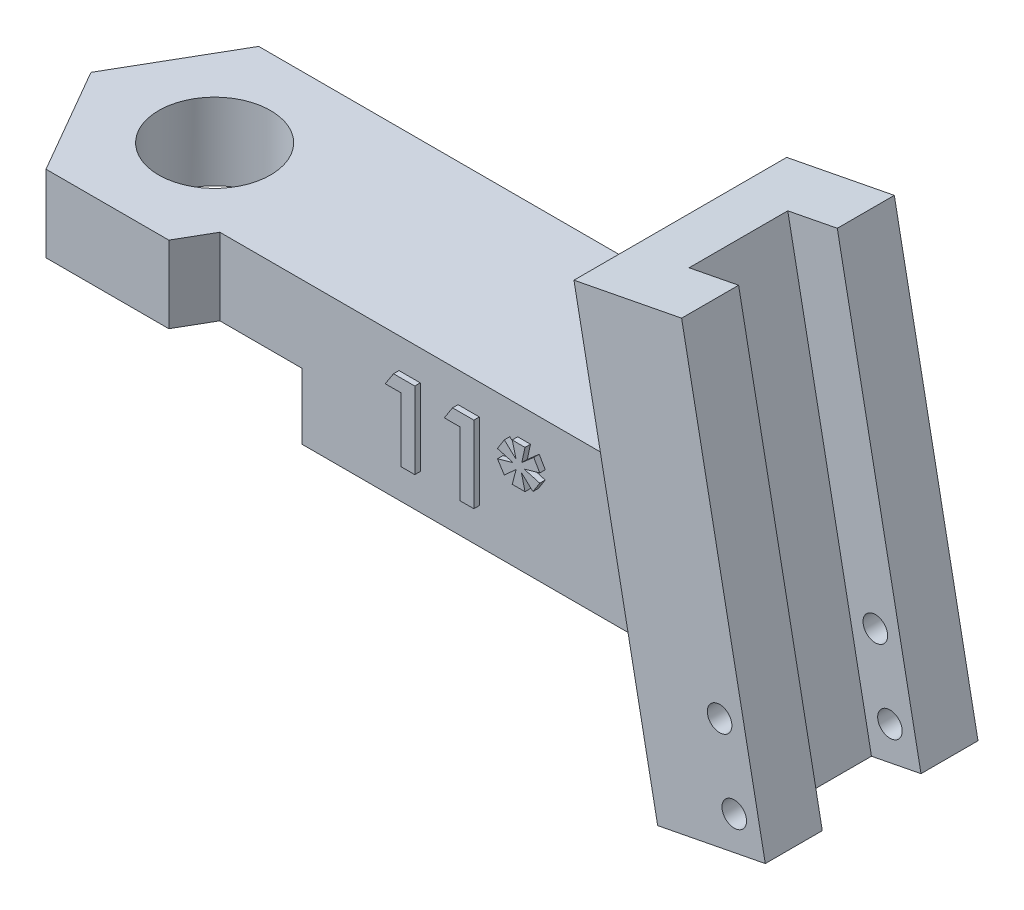
SolidWorks part; units mm, degrees
ref_plane "Front Plane" through (0, 0, 0) normal (0, 0, 1) x (1, 0, 0)
ref_plane "Top Plane" through (0, 0, 0) normal (0, 1, 0) x (1, 0, 0)
ref_plane "Right Plane" through (0, 0, 0) normal (1, 0, 0) x (0, 0, -1)
sketch "Sketch1" plane through (0, 0, 0) normal (0, 1, 0) x (1, 0, 0)
  line L1 (0, 0) -> (25, 0)
  line L2 (0, 0) -> (0, -6.75)
  line L3 (0, -6.75) -> (25, -6.75)
  line L4 (25, 0) -> (25, -6.75)
  dimension "D1" = 6.75
  dimension "D2" = 25
extrude "Boss-Extrude1" add sketch "Sketch1" along normal blind 6.5
ref_plane "Plane1" through (0, 0, 3.375) normal (0, 0, 1) x (1, 0, 0)
sketch "Sketch5" plane through (0, 6.5, 0) normal (0, 1, 0) x (1, 0, 0)
  line L0 (0, 0) -> (0, -6.75) construction
  line L1 (-5.6003, -3.375) -> (-2.8001, -8.225)
  line L2 (-2.8001, -8.225) -> (2.8001, -8.225)
  line L3 (2.8001, -8.225) -> (5.6003, -3.375)
  line L4 (5.6003, -3.375) -> (2.8001, 1.475)
  line L5 (2.8001, 1.475) -> (-2.8001, 1.475)
  line L6 (-2.8001, 1.475) -> (-5.6003, -3.375)
  circle A0 centre (0, -3.375) radius 4.85 construction
  dimension "D1" = 4.85
extrude "Boss-Extrude4" add sketch "Sketch5" against normal up to surface (6.5 mm away) up to face at (12.5, 0, 3.375)
sketch "Sketch3" plane through (0, 0, 3.375) normal (0, 0, 1) x (1, 0, 0)
  line L0 (21.2757, 14.1555) -> (26.1838, 15.1096)
  line L1 (26.1838, 15.1096) -> (30, -4.523)
  line L2 (30, -4.523) -> (25.0919, -5.477)
  line L3 (25.0919, -5.477) -> (21.2757, 14.1555)
  line L4 (3.6517, 6.5) -> (25, 6.5) construction
  point P6 (27.5459, -5)
  dimension "D1" = 30
  dimension "D2" = 5
  dimension "D3" = 20
  dimension "D4" = 79
  dimension "D6" = 5
extrude "Boss-Extrude3" add sketch "Sketch3" against normal up to surface and the other way up to surface up to face at (0, 3.25, -1.475) other way up to face at (0, 3.25, 8.225)
sketch "Sketch4" plane through (-1.8768, 9.6551, 0) normal (-0.1908, 0.9816, 0) x (0.9816, 0.1908, 0)
  line L0 (28.5858, -8.225) -> (28.5858, 1.475) construction
  line L1 (26.2858, -1.125) -> (28.5858, -1.125)
  line L2 (26.2858, -1.125) -> (26.2858, -5.625)
  line L3 (26.2858, -5.625) -> (28.5858, -5.625)
  line L4 (28.5858, -1.125) -> (28.5858, -5.625)
  point P6 (28.5858, -3.375)
  dimension "D1" = 4.5
  dimension "D2" = 2.3
extrude "Cut-Extrude1" cut sketch "Sketch4" against normal blind 23 contours L2 L3 L4 L1
sketch "Sketch6" plane through (0, 6.5, 0) normal (0, 1, 0) x (1, 0, 0)
  circle A0 centre (0, -3.3356) radius 2.55
  dimension "D1" = 5.1
extrude "Cut-Extrude2" cut sketch "Sketch6" against normal blind 10
sketch "Sketch7" plane through (0, 0, -1.475) normal (0, 0, -1) x (-1, 0, 0)
  line L0 (-2.8001, 0) -> (-24.0272, 0)
  line L1 (-24.0272, 0) -> (-25.0919, -5.477)
  line L2 (-25.0919, -5.477) -> (-30, -4.523)
  line L3 (-30, -4.523) -> (-26.1838, 15.1096)
  line L4 (-26.1838, 15.1096) -> (-21.2757, 14.1555)
  line L5 (-21.2757, 14.1555) -> (-22.7638, 6.5)
  line L6 (-22.7638, 6.5) -> (-2.8001, 6.5)
  line L7 (-2.8001, 6.5) -> (-2.8001, 0)
  dimension "D1" = 20
extrude "Boss-Extrude5" add sketch "Sketch7" against normal up to surface (1.475 mm away) up to face at (13.5236, 3.25, 0)
sketch "Sketch8" plane through (0, 0, 0) normal (0, -1, 0) x (-1, 0, 0)
  line L1 (-4.6765, -11.475) -> (4.6765, -11.475)
  line L2 (4.6765, -11.475) -> (9.3531, -3.375)
  line L3 (9.3531, -3.375) -> (4.6765, 4.725)
  line L4 (4.6765, 4.725) -> (-4.6765, 4.725)
  line L5 (-4.6765, 4.725) -> (-9.3531, -3.375)
  line L6 (-9.3531, -3.375) -> (-4.6765, -11.475)
  circle A0 centre (0, -3.375) radius 8.1 construction
  dimension "D1" = 16.2
extrude "Cut-Extrude3" cut sketch "Sketch8" against normal blind 3
sketch "Sketch9" plane through (0, 0, -1.475) normal (0, 0, -1) x (-1, 0, 0)
  line L0 (-30, -4.523) -> (-26.1838, 15.1096) construction
  line L1 (-25.0919, -5.477) -> (-30, -4.523) construction
  circle A0 centre (-28.5849, -3.27) radius 0.56
  circle A1 centre (-27.9171, 0.1657) radius 0.56
  dimension "D1" = 1.12
  dimension "D2" = 1.15
  dimension "D5" = 1.12
  dimension "D3" = 1.5
  dimension "D4" = 5
  dimension "D6" = 1.15
extrude "Cut-Extrude4" cut sketch "Sketch9" against normal up to surface (9.7 mm away) up to face at (25.6378, 4.8163, 8.225)
sketch "Sketch10" plane through (0, 0, 6.75) normal (0, 0, 1) x (1, 0, 0)
  text T0 "<b>11*</b>"
extrude "Boss-Extrude6" add sketch "Sketch10" along normal blind 0.25
